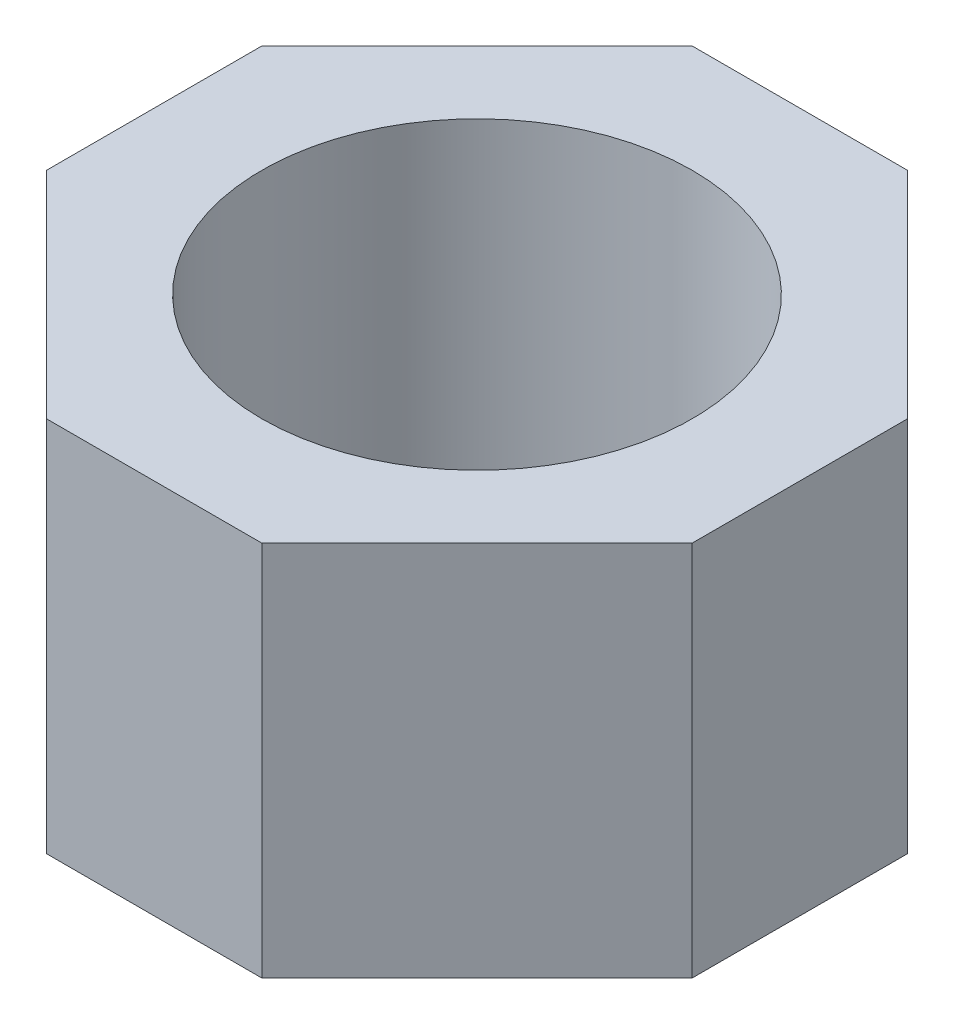
SolidWorks part; units mm, degrees
ref_plane "Front Plane" through (0, 0, 0) normal (0, 0, 1) x (1, 0, 0)
ref_plane "Top Plane" through (0, 0, 0) normal (0, 1, 0) x (1, 0, 0)
ref_plane "Right Plane" through (0, 0, 0) normal (1, 0, 0) x (0, 0, -1)
sketch "Sketch1" plane through (0, 0, 0) normal (0, 1, 0) x (1, 0, 0)
  line L0 (30, 10) -> (10, 30)
  line L1 (10, 30) -> (-10, 30)
  line L2 (30, 10) -> (30, -10)
  line L3 (10, -30) -> (-10, -30)
  line L4 (-30, 10) -> (-30, -10)
  line L5 (30, 30) -> (-30, -30) construction
  line L6 (30, -30) -> (-30, 30) construction
  line L7 (30, -10) -> (10, -30)
  line L8 (-10, -30) -> (-30, -10)
  line L9 (-10, 30) -> (-30, 10)
  point P0 (0, 0)
  point P14 (13.0283, 30)
  dimension "D1" = 60
  dimension "D2" = 60
extrude "Boss-Extrude1" add sketch "Sketch1" along normal blind 35
sketch "Sketch2" plane through (0, 35, 0) normal (0, 1, 0) x (1, 0, 0)
  circle A0 centre (0, 0) radius 20
  dimension "D1" = 40
extrude "Cut-Extrude1" cut sketch "Sketch2" against normal through all
